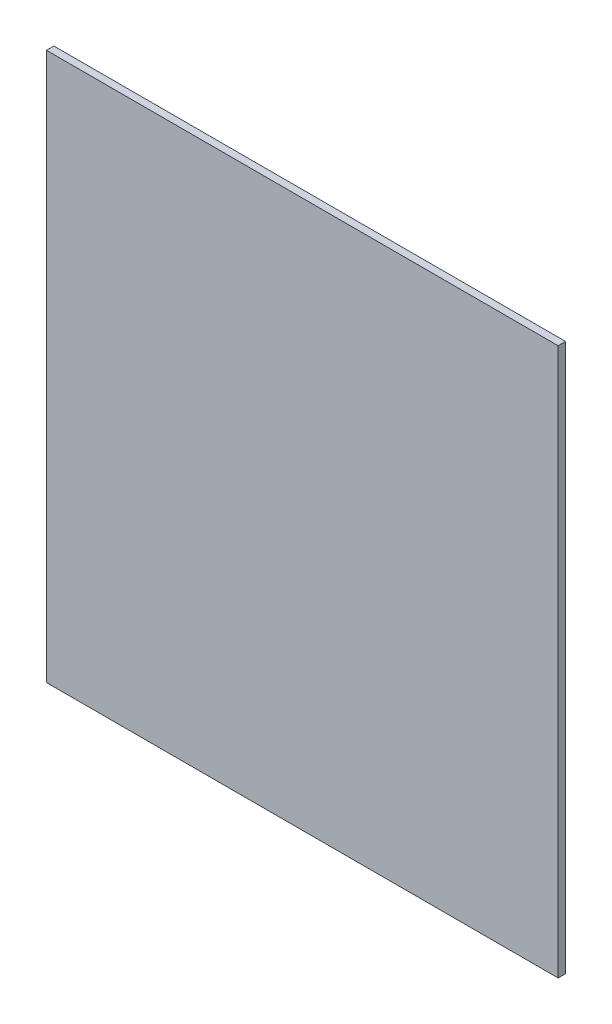
SolidWorks part; units mm, degrees
ref_plane "Plano frontal" through (0, 0, 0) normal (0, 0, 1) x (1, 0, 0)
ref_plane "Plano superior" through (0, 0, 0) normal (0, 1, 0) x (1, 0, 0)
ref_plane "Plano direito" through (0, 0, 0) normal (1, 0, 0) x (0, 0, -1)
sketch "Esboço1" plane through (0, 0, 0) normal (0, 0, 1) x (1, 0, 0)
  line L1 (-100, 107) -> (100, 107)
  line L2 (-100, 107) -> (-100, -107)
  line L3 (-100, -107) -> (100, -107)
  line L4 (100, 107) -> (100, -107)
  line L5 (-100, 107) -> (100, -107) construction
  line L6 (-100, -107) -> (100, 107) construction
  point P0 (0, 0)
  dimension "D1" = 200
  dimension "D2" = 214
extrude "Ressalto-extrusão1" add sketch "Esboço1" along normal blind 2.9
ref_plane "Plano1" through (0, 0, 0) normal (-1, 0, 0) x (0, 0, 1)
ref_plane "Plano2" through (0, 0, 0) normal (0, -1, 0) x (-1, 0, 0)
